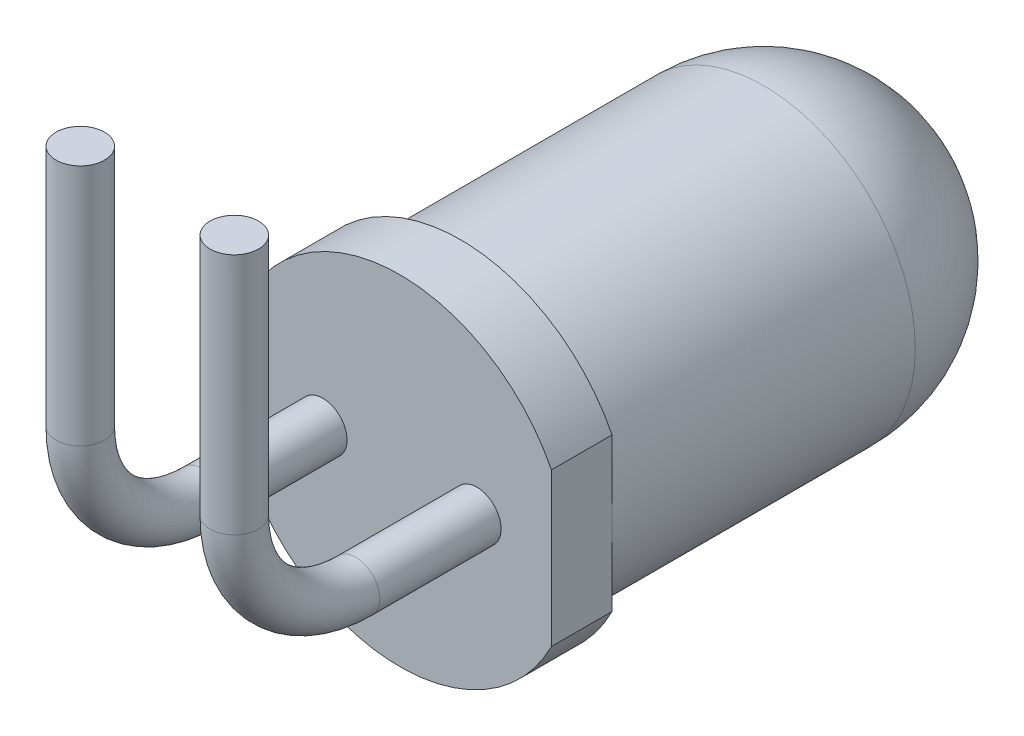
SolidWorks part; units mm, degrees
ref_plane "Face" through (0, 0, 0) normal (0, 0, 1) x (1, 0, 0)
ref_plane "Dessus" through (0, 0, 0) normal (0, 1, 0) x (1, 0, 0)
ref_plane "Droite" through (0, 0, 0) normal (1, 0, 0) x (0, 0, -1)
sketch "Esquisse1" plane through (0, 0, 0) normal (0, 0, 1) x (1, 0, 0)
  circle A0 centre (0, 0) radius 2.5
extrude "Base-Extrusion" add sketch "Esquisse1" along normal blind 8.5
sketch "Esquisse2" plane through (0, 0, 8.5) normal (0, 0, 1) x (1, 0, 0)
  line L0 (2.5, -2.4917) -> (2.5, 2.5621) construction
  line L1 (2.5, 1.261) -> (2.5, -1.261)
  arc A0 (2.5, 1.261) -> (2.5, -1.261) centre (0, 0) ccw
extrude "Boss.-Extru.1" add sketch "Esquisse2" against normal blind 1
fillet "Congé1" radius 2.5 1 edges at (2.5, 0, 0)
sketch "Esquisse3" plane through (0, 0, 8.5) normal (0, 0, 1) x (1, 0, 0)
  line L0 (2.8791, 0) -> (-3.5821, 0) construction
  line L1 (0, -2.9335) -> (0, 2.9813) construction
  line L2 (1.27, -0.8777) -> (1.27, 1.5607) construction
  circle A0 centre (1.27, 0) radius 0.4
  dimension "D1" = 1.27
ref_plane "Plan1" through (1.27, 0, 0) normal (1, 0, 0) x (0, 0, -1)
sketch "Esquisse5" plane through (1.27, 0, 0) normal (1, 0, 0) x (0, 0, -1)
  line L0 (-8.5, -5.3883) -> (-8.5, 4.4127) construction
  line L1 (-12.5, 9.2152) -> (-12.5, -2.555) construction
  line L2 (1.3145, 0) -> (-22.6036, 0) construction
  line L3 (-22.6036, 6) -> (-1.4343, 6) construction
  line L4 (-8.5, 0) -> (-10.5, 0)
  line L5 (-12.5, 6) -> (-12.5, 2)
  arc A0 (-10.5, 0) -> (-12.5, 2) centre (-10.5, 2) cw
  point P13 (-12.5, 0)
  dimension "D3" = 2
  dimension "D1" = 4
  dimension "D2" = 6
ref_plane "Plan2" through (0, 0, 0) normal (1, 0, 0) x (0, 0, -1)
sweep "Balayage1" add profiles "Esquisse3" path "Esquisse5"
mirror "Symétrie1" about plane through (0, 0, 0) normal (1, 0, 0) of "Balayage1"
